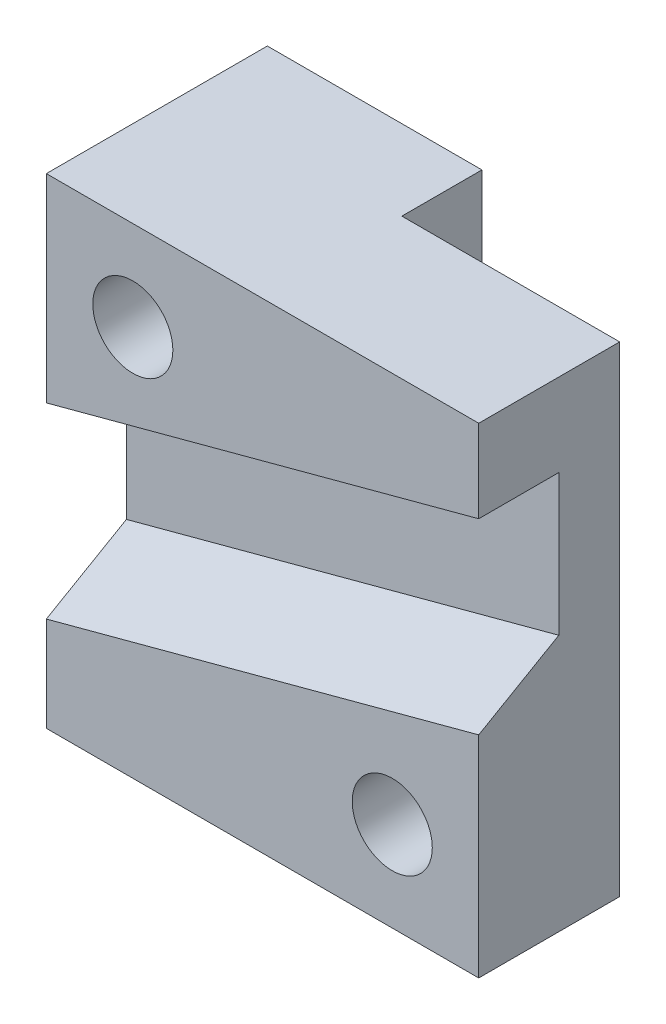
SolidWorks part; units mm, degrees
ref_plane "Front Plane" through (0, 0, 0) normal (0, 0, 1) x (1, 0, 0)
ref_plane "Top Plane" through (0, 0, 0) normal (0, 1, 0) x (1, 0, 0)
ref_plane "Right Plane" through (0, 0, 0) normal (1, 0, 0) x (0, 0, -1)
sketch "Sketch1" plane through (0, 0, 0) normal (0, 1, 0) x (1, 0, 0)
  line L0 (0, 0) -> (0, -22.352)
  line L1 (0, -22.352) -> (-68.58, -22.352)
  line L2 (-68.58, -22.352) -> (-68.58, 12.7)
  line L3 (-68.58, 12.7) -> (-34.544, 12.7)
  line L4 (-34.544, 12.7) -> (-34.544, 0)
  line L5 (-34.544, 0) -> (0, 0)
  dimension "D1" = 34.036
  dimension "D2" = 35.052
  dimension "D3" = 68.58
  dimension "D4" = 22.352
extrude "Boss-Extrude1" add sketch "Sketch1" along normal blind 76.2
sketch "Sketch2" plane through (-68.58, 0, 0) normal (-1, 0, 0) x (0, 0, 1)
  line L0 (22.352, 44.704) -> (9.652, 44.704)
  line L1 (22.352, 76.2) -> (22.352, 0) construction
  line L2 (9.652, 44.704) -> (9.652, 22.352)
  line L3 (9.652, 22.352) -> (22.352, 15.0197)
  line L4 (22.352, 76.2) -> (22.352, 44.704)
  line L5 (22.352, 15.0197) -> (22.352, 44.704)
  dimension "D1" = 120
  dimension "D2" = 22.352
  dimension "D3" = 12.7
  dimension "D4" = 31.496
sketch "Sketch4" plane through (0, 0, 22.352) normal (0, 0, 1) x (1, 0, 0)
  line L0 (-68.58, 44.704) -> (0, 63.08) construction
  line L1 (-68.58, 76.2) -> (-68.58, 0) construction
  line L2 (0, 76.2) -> (0, 0) construction
  line L3 (-68.58, 76.2) -> (0, 76.2) construction
  dimension "D1" = 15
extrude "Cut-Extrude1" cut sketch "Sketch2" along direction (0.9659, 0.2588, 0) on the side against the normal up to surface (70.9992 mm away) contours L0 L2 L3 L5
sketch "Sketch5" plane through (0, 0, 22.352) normal (0, 0, 1) x (1, 0, 0)
  line L0 (0, 33.3956) -> (0, 0) construction
  line L2 (-68.58, 0) -> (0, 0) construction
  circle A0 centre (-54.864, 61.976) radius 6.35
  circle A1 centre (-13.716, 14.224) radius 6.35
  dimension "D1" = 12.7
  dimension "D2" = 47.752
  dimension "D3" = 13.716
  dimension "D4" = 14.224
  dimension "D5" = 41.148
extrude "Cut-Extrude2" cut sketch "Sketch5" against normal through all
